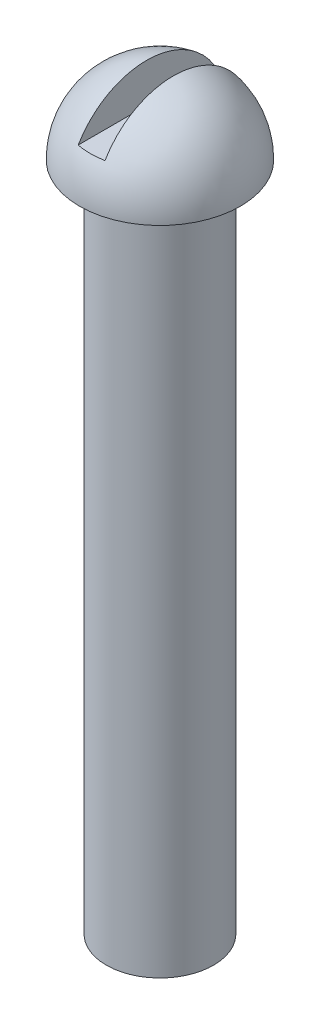
SolidWorks part; units mm, degrees
ref_plane "Front Plane" through (0, 0, 0) normal (0, 0, 1) x (1, 0, 0)
ref_plane "Top Plane" through (0, 0, 0) normal (0, 1, 0) x (1, 0, 0)
ref_plane "Right Plane" through (0, 0, 0) normal (1, 0, 0) x (0, 0, -1)
sketch "Sketch1" plane through (0, 0, 0) normal (0, 0, 1) x (1, 0, 0)
  line L0 (0, 0) -> (0, -40.4438) construction
  line L1 (0, 0) -> (3, 0)
  line L2 (0, 0) -> (2, 0)
  line L3 (0, 0) -> (0, -25)
  line L4 (0, -25) -> (2, -25)
  line L5 (2, 0) -> (2, -25)
  line L6 (0, 3) -> (0, 0)
  arc A0 (3, 0) -> (0, 3) centre (0, 0) ccw
  dimension "D1" = 25
  dimension "D2" = 2
  dimension "D3" = 3
revolve "Revolve1" add sketch "Sketch1" angle 360 about L6
sketch "Sketch2" plane through (0, 0, 0) normal (0, 0, 1) x (1, 0, 0)
  line L0 (0, 0) -> (0, 3) construction
  line L1 (-0.5, 1.5) -> (-0.5, 3.1427)
  line L2 (-0.5, 1.5) -> (0.5, 1.5)
  line L3 (0, 1.5) -> (0, 3.1427)
  line L4 (-0.5, 3.1427) -> (0.5, 3.1427)
  line L5 (0.5, 1.5) -> (0.5, 3.1427)
  arc A0 (3, 0) -> (-3, 0) centre (0, 0) ccw construction
  dimension "D1" = 0.5
extrude "Cut-Extrude1" cut sketch "Sketch2" against normal through all both and the other way through all contours L4 L1 L2 L3 | L2 L5 L4 L3
